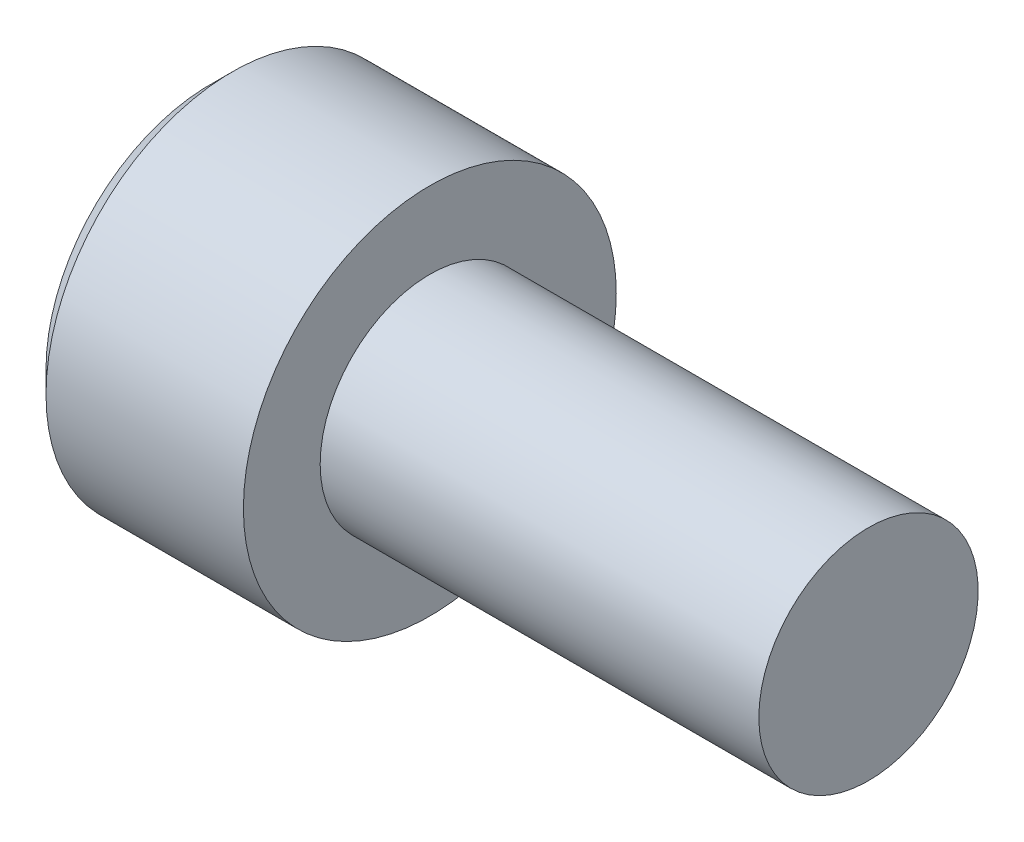
SolidWorks part; units mm, degrees
material "SCM435"
ref_plane "Front Plane" through (0, 0, 0) normal (0, 0, 1) x (1, 0, 0)
ref_plane "Top Plane" through (0, 0, 0) normal (0, 1, 0) x (1, 0, 0)
ref_plane "Right Plane" through (0, 0, 0) normal (1, 0, 0) x (0, 0, -1)
sketch "Sketch1" plane through (0, 0, 0) normal (0, 0, 1) x (1, 0, 0)
  line L2 (-5, 0) -> (10, 0)
  line L3 (10, 0) -> (10, 2.5)
  line L4 (10, 2.5) -> (0, 2.5)
  line L5 (0, 2.5) -> (0, 4.25)
  line L6 (0, 4.25) -> (-5, 4.25)
  line L7 (-5, 4.25) -> (-5, 0)
  line L8 (-5, 0) -> (10, 0) construction
  line L9 (0, 0) -> (0, 4.25) construction
  dimension "E" = 5
  dimension "L" = 10
  dimension "A" = 8.5
  dimension "M" = 5
revolve "Revolve1" add sketch "Sketch1" about L8
cosmetic thread "Thread1" parameters "L_s"=10, "ATD"=4.134
chamfer "Chamfer1" distance 0.5 1 edges at (-5, 0, 4.25)
sketch "Sketch2" plane through (0, 0, 0) normal (0, 0, 1) x (1, 0, 0)
  line L0 (-1.2983, 0) -> (-2.5, 2)
  line L1 (-5, 0) -> (10, 0) construction
  line L2 (-2.5, 2) -> (-5, 2)
  line L3 (-5, 4.25) -> (-5, 0) construction
  line L4 (-5, 2) -> (-5, 0)
  line L5 (-5, 0) -> (-1.2983, 0) construction
  line L6 (-1.2983, 0) -> (-5, 0)
  dimension "FIX_3" = 59
revolve "Cut-Revolve1" cut sketch "Sketch2" about L5
sketch "Sketch3" plane through (-5, 0, 0) normal (-1, 0, 0) x (0, 0, 1)
  line L0 (0, -2.3094) -> (0, 2.3094) construction
  line L1 (0, -2.3094) -> (2, -1.1547)
  line L2 (2, -1.1547) -> (2, 1.1547)
  line L3 (2, 1.1547) -> (0, 2.3094)
  line L4 (0, 2.3094) -> (-2, 1.1547)
  line L5 (-2, 1.1547) -> (-2, -1.1547)
  line L6 (-2, -1.1547) -> (0, -2.3094)
  line L7 (-2, 0) -> (2, 0) construction
  circle A0 centre (0, 0) radius 2 construction
extrude "Cut-Extrude1" cut sketch "Sketch3" against normal blind 2.5
